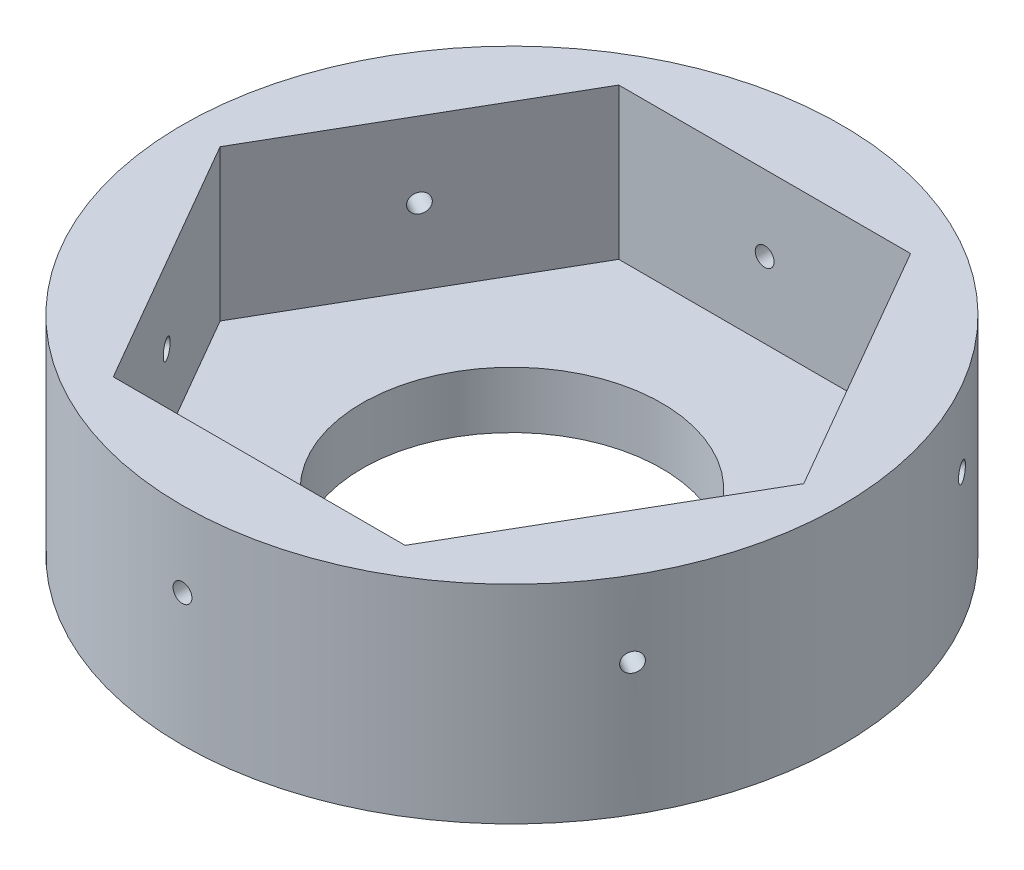
SolidWorks part; units mm, degrees
material "ABS"
ref_plane "Front Plane" through (0, 0, 0) normal (0, 0, 1) x (1, 0, 0)
ref_plane "Top Plane" through (0, 0, 0) normal (0, 1, 0) x (1, 0, 0)
ref_plane "Right Plane" through (0, 0, 0) normal (1, 0, 0) x (0, 0, -1)
sketch "Sketch1" plane through (0, 0, 0) normal (0, 1, 0) x (1, 0, 0)
  line L1 (38.6605, 66.962) -> (-38.6605, 66.962) construction
  line L2 (-38.6605, 66.962) -> (-77.321, 0) construction
  line L3 (-77.321, 0) -> (-38.6605, -66.962) construction
  line L4 (-38.6605, -66.962) -> (38.6605, -66.962) construction
  line L5 (38.6605, -66.962) -> (77.321, 0) construction
  line L6 (77.321, 0) -> (38.6605, 66.962) construction
  circle A1 centre (0, 0) radius 39.6875
  circle A2 centre (0, 0) radius 77.321
  dimension "D1" = 79.375
  dimension "D2" = 77.321
extrude "Boss-Extrude1" add sketch "Sketch1" along normal blind 15
sketch "Sketch2" plane through (0, 15, 0) normal (0, 1, 0) x (1, 0, 0)
  circle A0 centre (0, 0) radius 77.321 construction
  circle A4 centre (0, 0) radius 87.321
  circle A5 centre (0, 0) radius 77.321
  dimension "D1" = 10
extrude "Boss-Extrude2" add sketch "Sketch2" along normal blind 40 and the other way up to surface (15 mm away) other way up to face at (0, 0, 77.321)
sketch "Sketch3" plane through (0, 15, 0) normal (0, 1, 0) x (1, 0, 0)
  line L1 (77.321, 0) -> (38.6605, 66.962)
  line L2 (38.6605, 66.962) -> (-38.6605, 66.962)
  line L3 (-38.6605, 66.962) -> (-77.321, 0)
  line L4 (-77.321, 0) -> (-38.6605, -66.962)
  line L5 (-38.6605, -66.962) -> (38.6605, -66.962)
  line L6 (38.6605, -66.962) -> (77.321, 0)
  circle A0 centre (0, 0) radius 77.321 construction
  circle A1 centre (0, 0) radius 77.321 construction
extrude "Boss-Extrude3" add sketch "Sketch3" along normal up to surface (40 mm away)
sketch "Sketch4" plane through (0, 0, -66.962) normal (0, 0, 1) x (1, 0, 0)
  line L1 (-38.6605, 55) -> (-38.6605, 15) construction
  line L2 (38.6605, 55) -> (-38.6605, 55) construction
  circle A0 centre (0, 35) radius 2.5
  point P5 (-38.6605, 35)
  point P11 (0, 55)
  dimension "D1" = 5
extrude "Cut-Extrude1" cut sketch "Sketch4" against normal through all
pattern_circular "CirPattern1" count 6 over 360 about axis through (0, -246.9811, 0) along (0, 1, 0) of "Cut-Extrude1"
equation "\"Rope\"= 5in / 8"
equation "\"D1@Sketch1\"=\"Rope\"*5"
